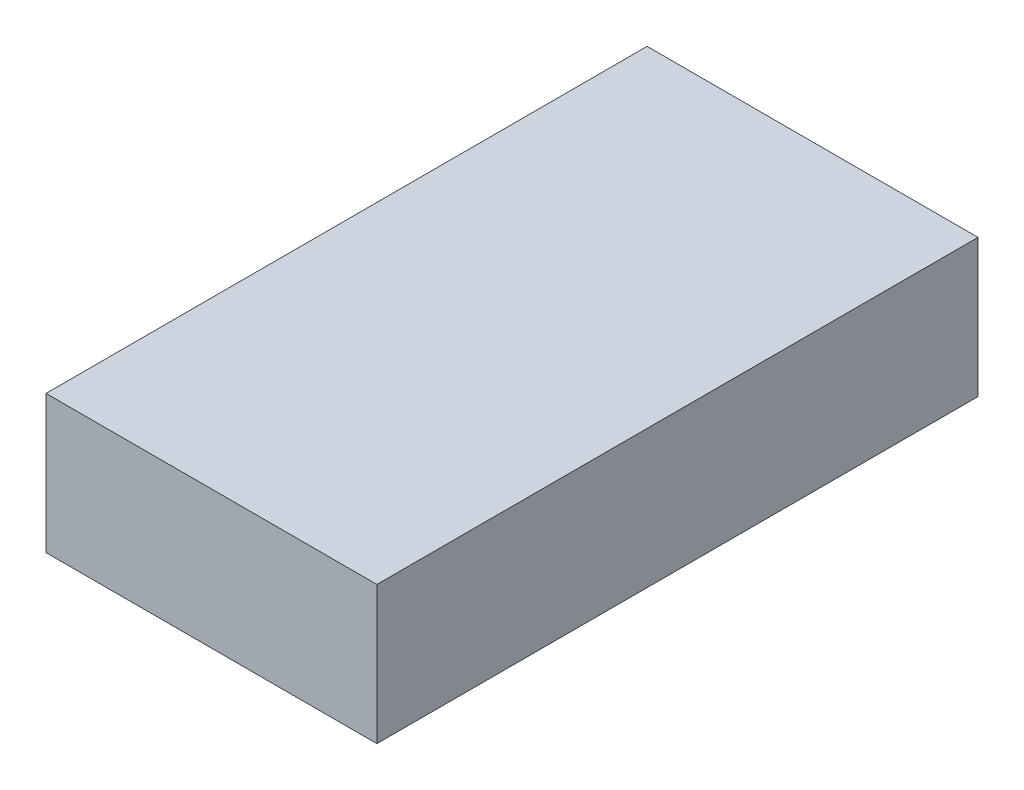
SolidWorks part; units mm, degrees
ref_plane "Alzado" through (0, 0, 0) normal (0, 0, 1) x (1, 0, 0)
ref_plane "Planta" through (0, 0, 0) normal (0, 1, 0) x (1, 0, 0)
ref_plane "Vista lateral" through (0, 0, 0) normal (1, 0, 0) x (0, 0, -1)
sketch "Croquis1" plane through (0, 0, 0) normal (0, 0, 1) x (1, 0, 0)
  line L1 (-7.146, 5) -> (-19.146, 5)
  line L2 (-7.146, 5) -> (-7.146, 0)
  line L3 (-7.146, 0) -> (-19.146, 0)
  line L4 (-19.146, 5) -> (-19.146, 0)
extrude "Saliente-Extruir1" add sketch "Croquis1" along normal blind 21.8
